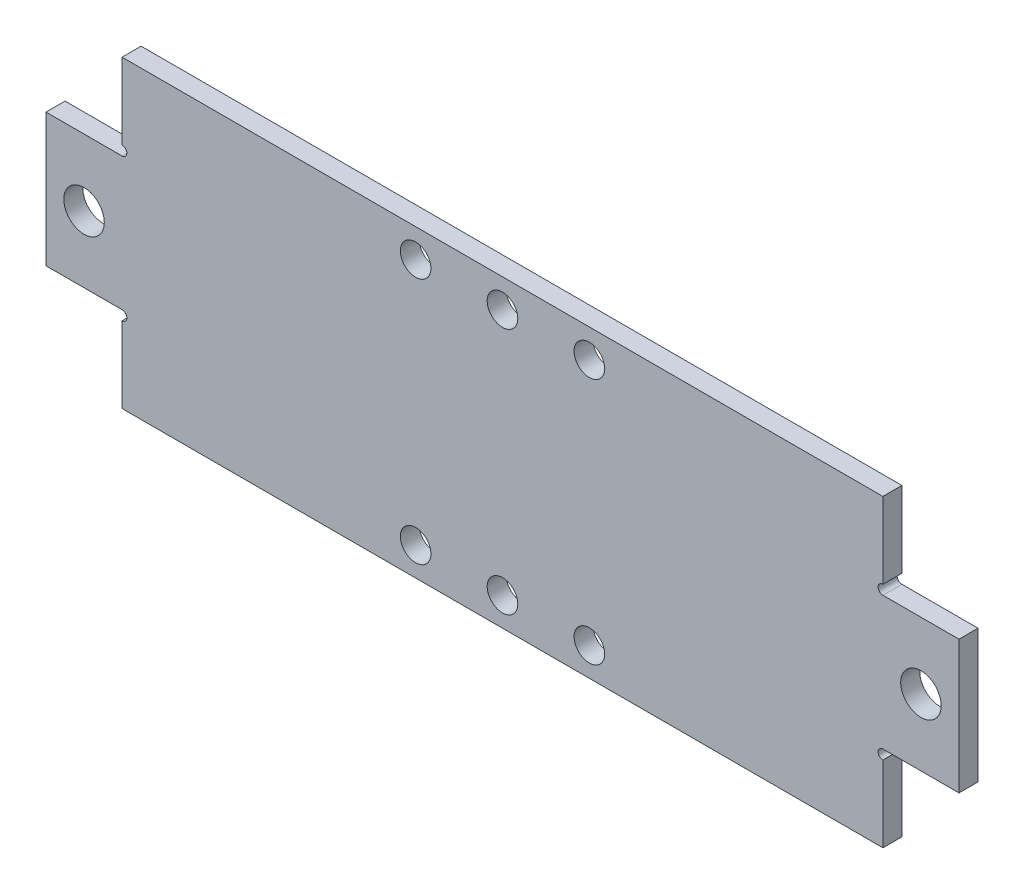
SolidWorks part; units mm, degrees
material "6061-T6 (SS)"
ref_plane "Front Plane" through (0, 0, 0) normal (0, 0, 1) x (1, 0, 0)
ref_plane "Top Plane" through (0, 0, 0) normal (0, 1, 0) x (1, 0, 0)
ref_plane "Right Plane" through (0, 0, 0) normal (1, 0, 0) x (0, 0, -1)
sketch "Sketch1" plane through (0, 0, 0) normal (0, 0, 1) x (1, 0, 0)
  line L1 (0, 0) -> (152.4, 0)
  line L2 (0, 0) -> (0, 50.8)
  line L3 (0, 50.8) -> (152.4, 50.8)
  line L4 (152.4, 0) -> (152.4, 50.8)
extrude "Boss-Extrude1" add sketch "Sketch1" along normal blind 3.175
sketch "Sketch2" plane through (0, 0, 3.175) normal (0, 0, 1) x (1, 0, 0)
  line L1 (0, 50.8) -> (12.7, 50.8)
  line L2 (0, 50.8) -> (0, 36.5125)
  line L3 (0, 36.5125) -> (12.7, 36.5125)
  line L4 (12.7, 50.8) -> (12.7, 36.5125)
  line L5 (0, 0) -> (12.7, 0)
  line L6 (0, 0) -> (0, 14.2875)
  line L7 (0, 14.2875) -> (12.7, 14.2875)
  line L8 (12.7, 0) -> (12.7, 14.2875)
  line L9 (152.4, 0) -> (139.7, 0)
  line L10 (152.4, 0) -> (152.4, 14.2875)
  line L11 (152.4, 14.2875) -> (139.7, 14.2875)
  line L12 (139.7, 0) -> (139.7, 14.2875)
  line L13 (152.4, 50.8) -> (139.7, 50.8)
  line L14 (152.4, 50.8) -> (152.4, 36.5125)
  line L15 (152.4, 36.5125) -> (139.7, 36.5125)
  line L16 (139.7, 50.8) -> (139.7, 36.5125)
  dimension "D1" = 12.7
  dimension "D2" = 22.225
extrude "Cut-Extrude1" cut sketch "Sketch2" against normal through all
sketch "Sketch3" plane through (0, 0, 3.175) normal (0, 0, 1) x (1, 0, 0)
  line L0 (12.7, 36.5125) -> (12.7, 50.8) construction
  line L1 (12.7, 0) -> (12.7, 14.2875) construction
  line L2 (139.7, 14.2875) -> (139.7, 0) construction
  line L3 (139.7, 50.8) -> (139.7, 36.5125) construction
  circle A0 centre (12.7, 37.3062) radius 0.7937
  circle A1 centre (12.7, 13.4938) radius 0.7937
  circle A2 centre (139.7, 13.4937) radius 0.7938
  circle A3 centre (139.7, 37.3062) radius 0.7938
  dimension "D1" = 1.5875
extrude "Cut-Extrude2" cut sketch "Sketch3" against normal through all
hole_wizard "1/4 Clearance Hole1" positions "Sketch5" profile "Sketch4" hole size "1/4" standard "ANSI Inch" end condition through all
sketch "Sketch5" plane through (0, 0, 3.175) normal (0, 0, 1) x (1, 0, 0)
  line L0 (0, 25.4) -> (6.35, 25.4) construction
  line L1 (0, 36.5125) -> (0, 14.2875) construction
  line L2 (6.35, 25.4) -> (6.35, 36.5125) construction
  line L3 (0, 36.5125) -> (12.7, 36.5125) construction
  line L4 (6.35, 36.5125) -> (146.05, 36.5125) construction
  line L5 (139.7, 36.5125) -> (152.4, 36.5125) construction
  line L6 (146.05, 36.5125) -> (146.05, 25.4) construction
  line L7 (146.05, 25.4) -> (152.4, 25.4) construction
  line L8 (152.4, 14.2875) -> (152.4, 36.5125) construction
  point P0 (6.35, 25.4)
  point P2 (146.05, 25.4)
sketch "Sketch4" plane through (6.35, 25.4, 3.175) normal (1, 0, 0) x (0, -1, 0)
  line L0 (0, 0) -> (0, 3.175)
  line L1 (0, 3.175) -> (3.3782, 3.175)
  line L2 (3.3782, 3.175) -> (3.3782, 0)
  line L5 (3.3782, 0) -> (0, 0)
  line L11 (0, -6.35) -> (0, 107.95) construction
  dimension "Thru Hole Dia." = 6.7564
  dimension "Thru Hole Depth" = 3.175
hole_wizard "#10 Clearance Hole1" positions "Sketch7" profile "Sketch6" hole size "#10" standard "ANSI Inch" end condition through all
sketch "Sketch7" plane through (0, 0, 3.175) normal (0, 0, 1) x (1, 0, 0)
  line L0 (61.7, 46.0375) -> (76.2, 46.0375) construction
  line L1 (76.2, 46.0375) -> (90.7, 46.0375) construction
  line L2 (90.7, 46.0375) -> (90.7, 4.7625) construction
  line L3 (90.7, 4.7625) -> (76.2, 4.7625) construction
  line L4 (76.2, 4.7625) -> (61.7, 4.7625) construction
  line L6 (12.7, 0) -> (139.7, 0) construction
  line L7 (76.2, 0) -> (76.2, 4.7625) construction
  line L8 (76.2, 4.7625) -> (76.2, 46.0375) construction
  line L9 (76.2, 46.0375) -> (76.2, 50.8) construction
  line L10 (139.7, 50.8) -> (12.7, 50.8) construction
  line L12 (61.7, 4.7625) -> (61.7, 46.0375) construction
  point P0 (76.2, 4.7625)
  point P2 (90.7, 4.7625)
  point P4 (61.7, 4.7625)
  point P6 (61.7, 46.0375)
  point P8 (76.2, 46.0375)
  point P10 (90.7, 46.0375)
  dimension "D1" = 14.5
  dimension "D2" = 4.7625
sketch "Sketch6" plane through (76.2, 4.7625, 3.175) normal (1, 0, 0) x (0, -1, 0)
  line L0 (0, 0) -> (0, 3.175)
  line L1 (0, 3.175) -> (2.5527, 3.175)
  line L2 (2.5527, 3.175) -> (2.5527, 0)
  line L5 (2.5527, 0) -> (0, 0)
  line L11 (0, -6.35) -> (0, 107.95) construction
  dimension "Thru Hole Dia." = 5.1054
  dimension "Thru Hole Depth" = 3.175
